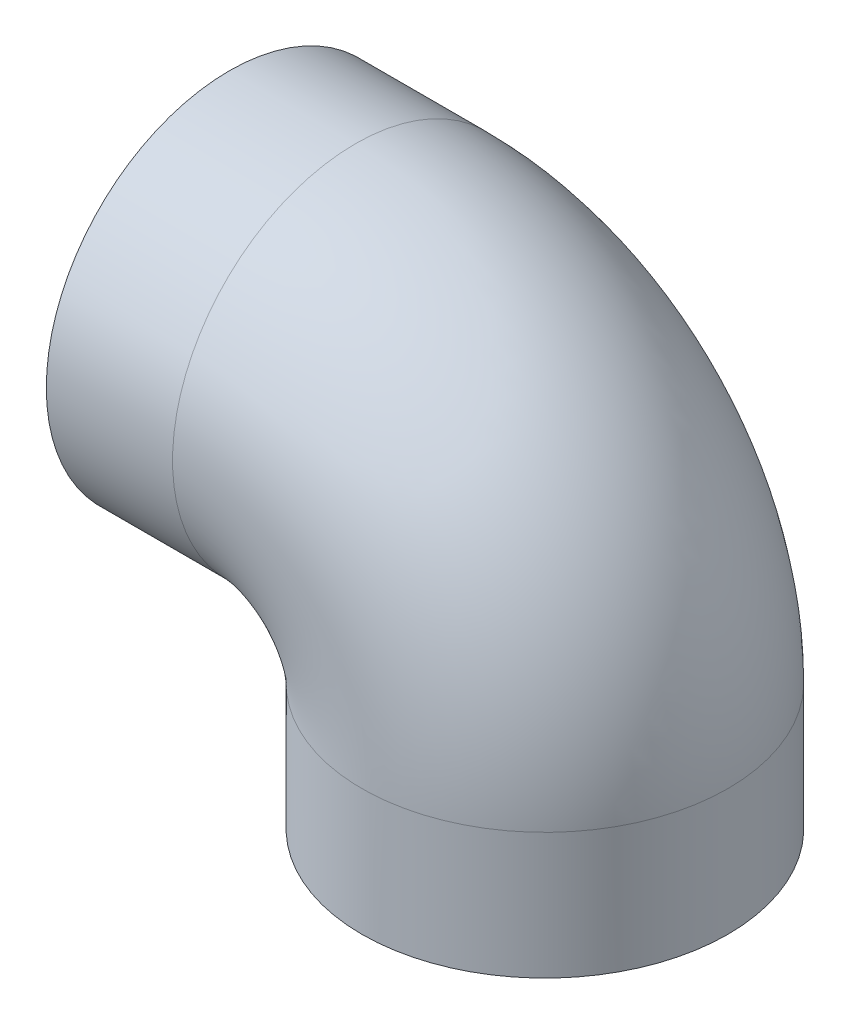
SolidWorks part; units mm, degrees
ref_plane "Front Plane" through (0, 0, 0) normal (0, 0, 1) x (1, 0, 0)
ref_plane "Top Plane" through (0, 0, 0) normal (0, 1, 0) x (1, 0, 0)
ref_plane "Right Plane" through (0, 0, 0) normal (1, 0, 0) x (0, 0, -1)
sketch "Sketch1" plane through (0, 0, 0) normal (0, 0, 1) x (1, 0, 0)
  line L0 (0, 30) -> (-20, 30)
  line L1 (30, 0) -> (30, -20)
  arc A0 (30, 0) -> (0, 30) centre (0, 0) ccw
  dimension "D1" = 30
  dimension "D2" = 20
  dimension "D3" = 20
ref_plane "Plane1" through (0, -20, 0) normal (0, 1, 0) x (1, 0, 0)
sketch "Sketch2" plane through (0, -20, 0) normal (0, 1, 0) x (1, 0, 0)
  circle A0 centre (30, 0) radius 29
  circle A1 centre (30, 0) radius 25
  dimension "D1" = 58
  dimension "D2" = 50
sweep "Sweep1" add profiles "Sketch2" path "Sketch1"
sketch "Sketch3" plane through (-20, 0, 0) normal (-1, 0, 0) x (0, 0, 1)
  circle A0 centre (0, 30) radius 27
  circle A1 centre (0, 30) radius 25
  dimension "D1" = 54
  dimension "D2" = 50
extrude "Cut-Extrude1" cut sketch "Sketch3" against normal blind 5
sketch "Sketch4" plane through (0, -20, 0) normal (0, -1, 0) x (1, 0, 0)
  circle A0 centre (30, 0) radius 25
  circle A1 centre (30, 0) radius 27
  dimension "D1" = 50
  dimension "D2" = 54
extrude "Cut-Extrude2" cut sketch "Sketch4" against normal blind 5
